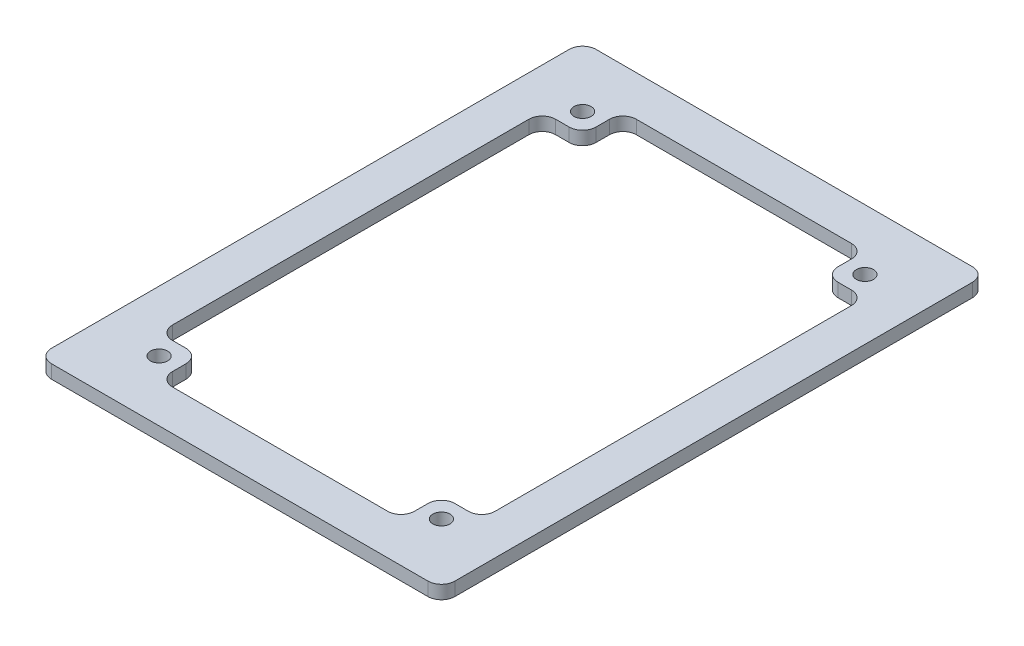
SolidWorks part; units mm, degrees
material "Thornel Mat VMA"
ref_plane "前视基准面" through (0, 0, 0) normal (0, 0, 1) x (1, 0, 0)
ref_plane "上视基准面" through (0, 0, 0) normal (0, 1, 0) x (1, 0, 0)
ref_plane "右视基准面" through (0, 0, 0) normal (1, 0, 0) x (0, 0, -1)
other "Configuration Table"
sketch "草图1" plane through (0, 0, 0) normal (0, 1, 0) x (1, 0, 0)
  line L7 (-24, -34.5) -> (24, -34.5)
  line L8 (-24, -34.5) -> (-24, 34.5)
  line L9 (-24, 34.5) -> (24, 34.5)
  line L10 (24, -34.5) -> (24, 34.5)
  line L11 (-24, -34.5) -> (24, 34.5) construction
  line L12 (-24, 34.5) -> (24, -34.5) construction
  point P0 (0, 0)
  point P6 (0, 0)
  dimension "D1" = 48
  dimension "D2" = 69
extrude "凸台-拉伸1" add sketch "草图1" along normal blind 2
sketch "草图2" plane through (0, 2, 0) normal (0, 1, 0) x (1, 0, 0)
  line L8 (30, -40.5) -> (30, 40.5)
  line L9 (30, 40.5) -> (-30, 40.5)
  line L10 (-30, 40.5) -> (-30, -40.5)
  line L11 (-30, -40.5) -> (30, -40.5)
  line L12 (30, -40.5) -> (30, 40.5)
  line L13 (30, 40.5) -> (-30, 40.5)
  line L14 (-30, 40.5) -> (-30, -40.5)
  line L15 (-30, -40.5) -> (30, -40.5)
  dimension "D1" = 6
extrude "凸台-拉伸2" add sketch "草图2" against normal up to surface (2 mm away) up to face at (0, 0, 0)
sketch "草图3" plane through (0, 2, 0) normal (0, 1, 0) x (1, 0, 0)
  line L8 (-24, -34.5) -> (24, -34.5)
  line L9 (24, -34.5) -> (24, 34.5)
  line L10 (24, 34.5) -> (-24, 34.5)
  line L11 (-24, 34.5) -> (-24, -34.5)
  line L12 (-24, -34.5) -> (24, -34.5)
  line L13 (24, -34.5) -> (24, 34.5)
  line L14 (24, 34.5) -> (-24, 34.5)
  line L15 (-24, 34.5) -> (-24, -34.5)
  dimension "D1" = 6
extrude "切除-拉伸1" cut sketch "草图3" against normal up to surface (2 mm away) up to face at (0, 0, 0)
sketch "草图4" plane through (0, 0, 0) normal (0, -1, 0) x (1, 0, 0)
  line L1 (-24, 34.5) -> (-18, 34.5)
  line L2 (-24, 34.5) -> (-24, 28.5)
  line L3 (-24, 28.5) -> (-18, 28.5)
  line L4 (-18, 34.5) -> (-18, 28.5)
  line L5 (24, 34.5) -> (18, 34.5)
  line L6 (24, 34.5) -> (24, 28.5)
  line L7 (24, 28.5) -> (18, 28.5)
  line L8 (18, 34.5) -> (18, 28.5)
  line L9 (-24, -34.5) -> (-18, -34.5)
  line L10 (-24, -34.5) -> (-24, -28.5)
  line L11 (-24, -28.5) -> (-18, -28.5)
  line L12 (-18, -34.5) -> (-18, -28.5)
  line L13 (24, -34.5) -> (18, -34.5)
  line L14 (24, -34.5) -> (24, -28.5)
  line L15 (24, -28.5) -> (18, -28.5)
  line L16 (18, -34.5) -> (18, -28.5)
  dimension "D1" = 6
extrude "凸台-拉伸3" add sketch "草图4" against normal up to surface (2 mm away) up to face at (0, 2, 0)
sketch "草图5" plane through (0, 0, 0) normal (0, -1, 0) x (1, 0, 0)
  line L0 (-18, 28.5) -> (-18, 34.5) construction
  line L1 (-24, 28.5) -> (-18, 28.5) construction
  line L2 (18, 28.5) -> (24, 28.5) construction
  line L3 (18, -28.5) -> (18, -34.5) construction
  circle A0 centre (-21, 31.5) radius 1.275
  circle A1 centre (-21, -31.5) radius 1.275
  circle A2 centre (21, -31.5) radius 1.275
  circle A3 centre (21, 31.5) radius 1.275
  point P11 (-18, 31.5)
  point P15 (-21, 28.5)
  point P19 (21, 28.5)
  point P22 (18, -31.5)
  dimension "D1" = 2.55
extrude "切除-拉伸2" cut sketch "草图5" against normal up to surface (2 mm away) up to face at (0, 2, 0)
fillet "圆角1" radius 2 16 edges at (30, 1, 40.5) (30, 1, -40.5) (-30, 1, 40.5) (24, 1, 28.5) (18, 1, 28.5) (18, 1, 34.5) (-18, 1, 34.5) (-18, 1, 28.5) (-24, 1, 28.5) (-24, 1, -28.5) (-18, 1, -28.5) (-18, 1, -34.5) (18, 1, -34.5) (18, 1, -28.5) (24, 1, -28.5) (-30, 1, -40.5)
